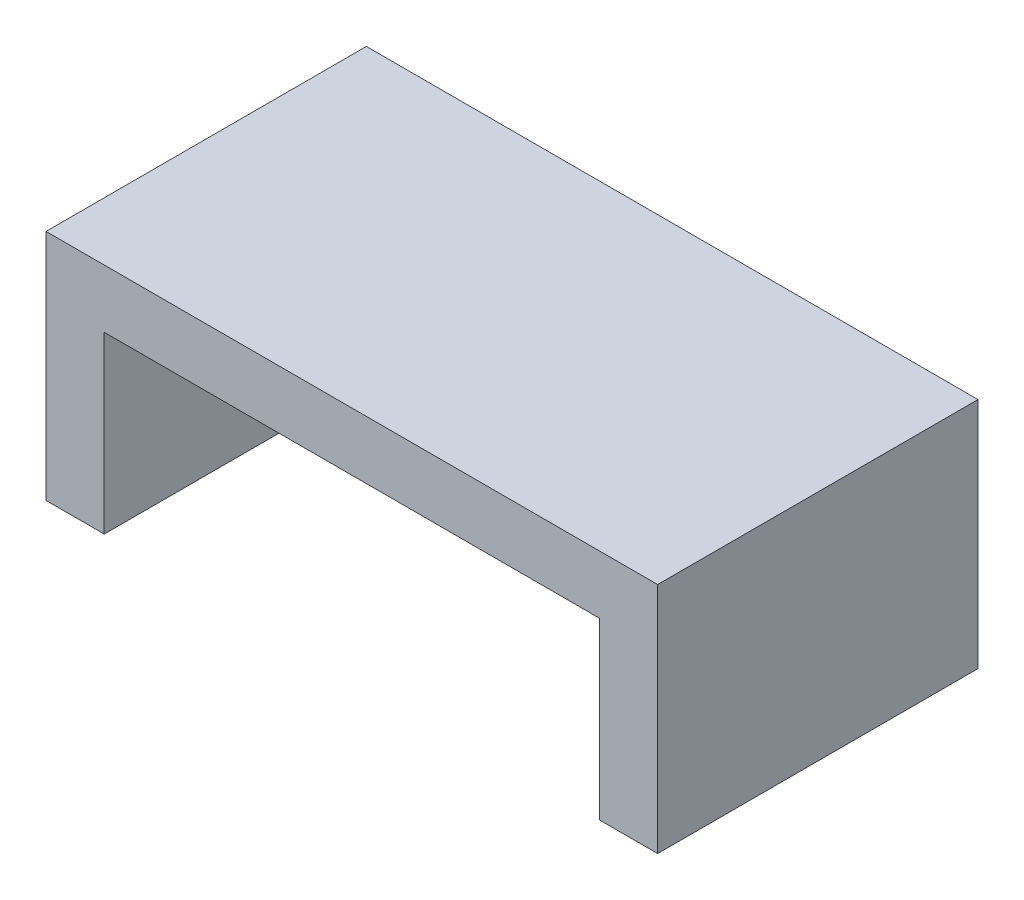
SolidWorks part; units mm, degrees
ref_plane "Front Plane" through (0, 0, 0) normal (0, 0, 1) x (1, 0, 0)
ref_plane "Top Plane" through (0, 0, 0) normal (0, 1, 0) x (1, 0, 0)
ref_plane "Right Plane" through (0, 0, 0) normal (1, 0, 0) x (0, 0, -1)
sketch "Sketch1" plane through (0, 0, 0) normal (0, 1, 0) x (1, 0, 0)
  line L1 (-18.3662, 12.4024) -> (23.6338, 12.4024)
  line L2 (-18.3662, 12.4024) -> (-18.3662, -9.5976)
  line L3 (-18.3662, -9.5976) -> (23.6338, -9.5976)
  line L4 (23.6338, 12.4024) -> (23.6338, -9.5976)
  dimension "D1" = 22
  dimension "D2" = 42
extrude "Boss-Extrude1" add sketch "Sketch1" along normal blind 16
shell "Shell2" thickness 4
sketch "Sketch2" plane through (0, 16, 0) normal (0, 1, 0) x (1, 0, 0)
  line L0 (23.6338, 12.4024) -> (-18.3662, 12.4024) construction
  line L1 (-5.1462, 12.4024) -> (10.4138, 12.4024)
  line L2 (-5.1462, 12.4024) -> (-5.1462, -9.5976)
  line L3 (-5.1462, -9.5976) -> (10.4138, -9.5976)
  line L4 (10.4138, 12.4024) -> (10.4138, -9.5976)
  line L5 (-18.3662, -9.5976) -> (23.6338, -9.5976) construction
  line L6 (-18.3662, 12.4024) -> (-18.3662, -9.5976) construction
  dimension "D1" = 15.56
  dimension "D2" = 13.22
equation "\"D2@Sketch2\"=(\"D2@Sketch1\"-\"D1@Sketch2\")/2"
